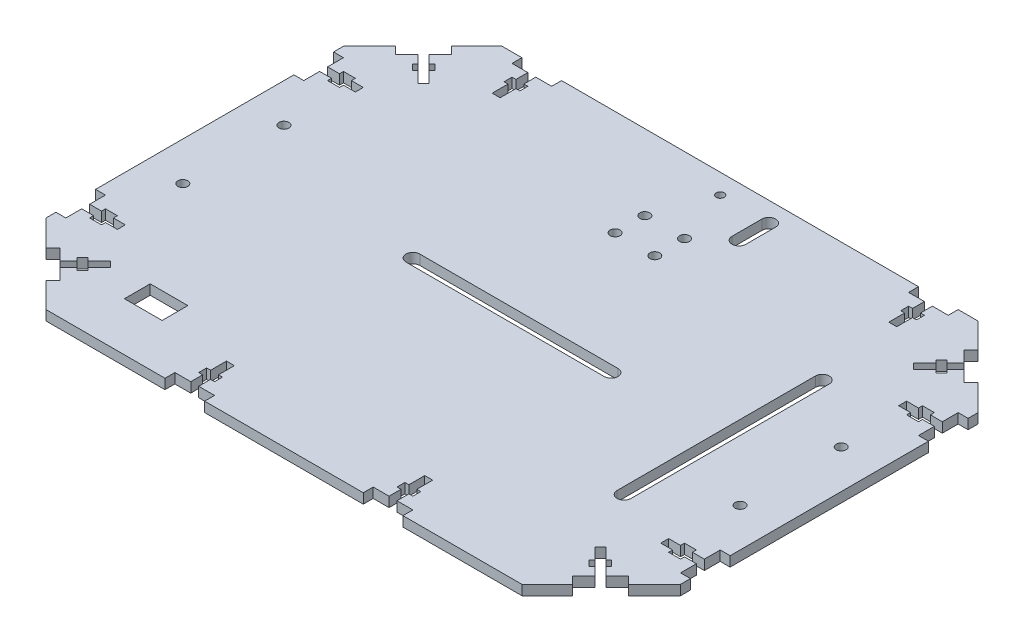
SolidWorks part; units mm, degrees
ref_plane "Front Plane" through (0, 0, 0) normal (0, 0, 1) x (1, 0, 0)
ref_plane "Top Plane" through (0, 0, 0) normal (0, 1, 0) x (1, 0, 0)
ref_plane "Right Plane" through (0, 0, 0) normal (1, 0, 0) x (0, 0, -1)
sketch "Sketch2" plane through (0, 0, 0) normal (0, 1, 0) x (1, 0, 0)
  line L1 (160, -115) -> (-160, -115)
  line L2 (160, -115) -> (160, 115)
  line L3 (160, 115) -> (-160, 115)
  line L4 (-160, -115) -> (-160, 115)
  line L5 (160, -115) -> (-160, 115) construction
  line L6 (160, 115) -> (-160, -115) construction
  point P0 (0, 0)
  dimension "D1" = 230
  dimension "D2" = 320
extrude "Boss-Extrude1" add sketch "Sketch2" along normal blind 5
chamfer "Chamfer1" distance 40 distance2 40 1 edges at (-160, 2.5, -115)
chamfer "Chamfer2" distance 40 distance2 40 1 edges at (160, 2.5, -115)
chamfer "Chamfer3" distance 40 distance2 40 1 edges at (-160, 2.5, 115)
chamfer "Chamfer4" distance 40 distance2 40 1 edges at (160, 2.5, 115)
sketch "Sketch3" plane through (0, 5, 0) normal (0, 1, 0) x (1, 0, 0)
  line L1 (-160, 75) -> (-160, -75) construction
  line L2 (120, 115) -> (-120, 115) construction
  circle A0 centre (-10, 77) radius 2.5
  circle A1 centre (-10, 62) radius 2.5
  dimension "D1" = 5
  dimension "D2" = 5
  dimension "D3" = 38
  dimension "D4" = 150
  dimension "D5" = 150
  dimension "D6" = 15
extrude "Cut-Extrude1" cut sketch "Sketch3" against normal blind 10
mirror "Mirror1" about plane through (0, 0, 0) normal (1, 0, 0) of "Cut-Extrude1"
sketch "Sketch10" plane through (0, 5, 0) normal (0, 1, 0) x (1, 0, 0)
  line L0 (40, -115) -> (60, -115)
  line L1 (40, -115) -> (40, -110)
  line L2 (40, -110) -> (60, -110)
  line L3 (60, -115) -> (60, -110)
  line L4 (48, -110) -> (52, -110)
  line L5 (48, -110) -> (48, -92)
  line L6 (48, -92) -> (52, -92)
  line L7 (52, -110) -> (52, -92)
  line L8 (46, -100) -> (54, -100)
  line L9 (46, -100) -> (46, -104)
  line L10 (46, -104) -> (54, -104)
  line L11 (54, -100) -> (54, -104)
  line L12 (-120, -115) -> (120, -115) construction
  line L13 (160, -75) -> (160, 75) construction
  dimension "D1" = 20
  dimension "D2" = 4
  dimension "D3" = 18
  dimension "D4" = 4
  dimension "D5" = 8
  dimension "D6" = 6
  dimension "D7" = 8
  dimension "D8" = 6
  dimension "D9" = 6
  dimension "D10" = 5
  dimension "D11" = 0
  dimension "D12" = 100
extrude "Cut-Extrude7" cut sketch "Sketch10" against normal blind 10 contours L10 L5 L2 L7 | L5 L10 L7 L8
mirror "Mirror2" about plane through (0, 0, 0) normal (1, 0, 0) of "Cut-Extrude7"
sketch "Sketch11" plane through (0, 5, 0) normal (0, 1, 0) x (1, 0, 0)
  line L1 (90, 115) -> (110, 115)
  line L2 (90, 115) -> (90, 110)
  line L3 (90, 110) -> (110, 110)
  line L4 (110, 115) -> (110, 110)
  line L6 (120, 115) -> (-120, 115) construction
  line L7 (98, 110) -> (102, 110)
  line L8 (98, 110) -> (98, 92)
  line L9 (98, 92) -> (102, 92)
  line L10 (102, 110) -> (102, 92)
  line L11 (96, 104) -> (104, 104)
  line L12 (96, 104) -> (96, 100)
  line L13 (96, 100) -> (104, 100)
  line L14 (104, 104) -> (104, 100)
  line L15 (160, -75) -> (160, 75) construction
  line M55 (120, 115) -> (-120, 115)
  dimension "D1" = 20
  dimension "D2" = 0
  dimension "D3" = 5
  dimension "D4" = 18
  dimension "D5" = 4
  dimension "D6" = 8
  dimension "D7" = 8
  dimension "D8" = 6
  dimension "D9" = 4
  dimension "D10" = 8
  dimension "D11" = 6
  dimension "D12" = 50
extrude "Cut-Extrude8" cut sketch "Sketch11" against normal blind 10 contours L4 L2 L3 M55 | L8 L11 L10 L3 | L8 L13 L10 L11 | L13 L8 L9 L10 | L14 L11 L10 L13 | L12 L13 L8 L11
mirror "Mirror3" about plane through (0, 0, 0) normal (1, 0, 0) of "Cut-Extrude8"
sketch "Sketch13" plane through (0, 5, 0) normal (0, 1, 0) x (1, 0, 0)
  line L0 (-160, 75) -> (-160, -75) construction
  line L1 (-160, -50) -> (-155, -50)
  line L2 (-160, -50) -> (-160, -70)
  line L3 (-160, -70) -> (-155, -70)
  line L4 (-155, -50) -> (-155, -70)
  line L5 (-120, -115) -> (-60, -115) construction
  line L7 (-155, -58) -> (-137, -58)
  line L8 (-155, -58) -> (-155, -62)
  line L9 (-155, -62) -> (-137, -62)
  line L10 (-137, -58) -> (-137, -62)
  line L11 (-149, -56) -> (-143, -56)
  line L12 (-149, -56) -> (-149, -64)
  line L13 (-149, -64) -> (-143, -64)
  line L14 (-143, -56) -> (-143, -64)
  dimension "D1" = 5
  dimension "D2" = 45
  dimension "D3" = 20
  dimension "D4" = 4
  dimension "D5" = 8
  dimension "D6" = 8
  dimension "D7" = 18
  dimension "D8" = 6
  dimension "D9" = 8
  dimension "D10" = 2
  dimension "D11" = 6
  dimension "D12" = 6
extrude "Cut-Extrude9" cut sketch "Sketch13" against normal blind 10 contours L4 L1 L2 L3 | L14 L9 L12 L13 | L14 L11 L12 L7
mirror "Mirror4" about plane through (0, 0, 0) normal (1, 0, 0) of "Cut-Extrude9" second plane through (0, 0, 0) second plane normal (0, 0, 1)
sketch "Sketch14" plane through (0, 5, 0) normal (0, 1, 0) x (1, 0, 0)
  line L0 (-146.8701, -88.1299) -> (-132.7279, -102.2721)
  line L2 (-132.7279, -102.2721) -> (-129.1924, -98.7365)
  line L3 (-129.1924, -98.7365) -> (-143.3345, -84.5944)
  line L4 (-143.3345, -84.5944) -> (-146.8701, -88.1299)
  line L5 (-134.8492, -93.0797) -> (-122.1213, -80.3518)
  line L6 (-122.1213, -80.3518) -> (-124.9497, -77.5233)
  line L7 (-124.9497, -77.5233) -> (-137.6777, -90.2513)
  line L8 (-134.8492, -84.5944) -> (-129.1924, -90.2513)
  line L9 (-134.8492, -84.5944) -> (-132.0208, -81.766)
  line L10 (-132.0208, -81.766) -> (-126.364, -87.4228)
  line L11 (-126.364, -87.4228) -> (-129.1924, -90.2513)
  line L12 (-160, -75) -> (-120, -115) construction
  dimension "D1" = 5
  dimension "D2" = 20
  dimension "D3" = 0
  dimension "D4" = 18
  dimension "D5" = 4
  dimension "D6" = 8
  dimension "D7" = 8
  dimension "D8" = 18
  dimension "D9" = 6
  dimension "D10" = 4
  dimension "D11" = 6
  dimension "D12" = 8
  dimension "D13" = 6
  dimension "D14" = 18.5685
extrude "Cut-Extrude10" cut sketch "Sketch14" against normal blind 10 contours L3 L4 L0 L2 | L8 L7 L3 L5 | L10 L7 L8 L5 | L7 L10 L5 L6 | L11 L10 L5 L8 | L10 L9 L8 L7
mirror "Mirror5" about plane through (0, 0, 0) normal (1, 0, 0) of "Cut-Extrude10" second plane through (0, 0, 0) second plane normal (0, 0, 1)
sketch "Sketch15" plane through (0, 5, 0) normal (0, 1, 0) x (1, 0, 0)
  line L0 (50, 0) -> (-50, 0) construction
  line L1 (50, -3.5) -> (-50, -3.5)
  line L2 (50, 3.5) -> (-50, 3.5)
  line L3 (160, -50) -> (160, 50) construction
  line L4 (-160, 50) -> (-160, -50) construction
  line L5 (-40, -115) -> (40, -115) construction
  line L6 (90, 115) -> (-90, 115) construction
  arc A0 (50, -3.5) -> (50, 3.5) centre (50, 0) ccw
  arc A1 (-50, 3.5) -> (-50, -3.5) centre (-50, 0) ccw
  point P3 (0, 0)
  dimension "D2" = 110
  dimension "D3" = 110
  dimension "D1" = 100
  dimension "D4" = 7
  dimension "D5" = 100
  dimension "D6" = 111.5
  dimension "D7" = 111.5
extrude "Cut-Extrude11" cut sketch "Sketch15" against normal blind 10
sketch "Sketch16" plane through (0, 5, 0) normal (0, 1, 0) x (1, 0, 0)
  line L0 (106.5, 50) -> (106.5, -50) construction
  line L1 (110, 50) -> (110, -50)
  line L2 (103, 50) -> (103, -50)
  line L5 (-110, 115) -> (-120, 115) construction
  line L7 (-120, -115) -> (-60, -115) construction
  line L9 (160, -50) -> (160, 50) construction
  arc A0 (110, 50) -> (103, 50) centre (106.5, 50) ccw
  arc A1 (103, -50) -> (110, -50) centre (106.5, -50) ccw
  point P2 (106.5, 0)
  dimension "D3" = 65
  dimension "D4" = 65
  dimension "D1" = 100
  dimension "D2" = 7
  dimension "D5" = 50
extrude "Cut-Extrude12" cut sketch "Sketch16" against normal blind 10
sketch "Sketch17" plane through (0, 5, 0) normal (0, 1, 0) x (1, 0, 0)
  line L0 (160, -50) -> (160, 50) construction
  line L1 (120, 115) -> (110, 115) construction
  circle A0 centre (140.5, 25.5) radius 2.5
  dimension "D1" = 5
  dimension "D2" = 19.5
  dimension "D3" = 89.5
extrude "Cut-Extrude13" cut sketch "Sketch17" against normal blind 10
mirror "Mirror6" about plane through (0, 0, 0) normal (1, 0, 0) of "Cut-Extrude13" second plane through (0, 0, 0) second plane normal (0, 0, 1)
sketch "Sketch18" plane through (0, 5, 0) normal (0, 1, 0) x (1, 0, 0)
  line L0 (90, 115) -> (-90, 115) construction
  circle A0 centre (0, 105) radius 2
  dimension "D1" = 4
  dimension "D2" = 10
extrude "Cut-Extrude14" cut sketch "Sketch18" against normal blind 8
sketch "Sketch19" plane through (0, 5, 0) normal (0, 1, 0) x (1, 0, 0)
  line L0 (24.4719, 105) -> (24.4719, 90) construction
  line L1 (27.9719, 105) -> (27.9719, 90)
  line L2 (20.9719, 105) -> (20.9719, 90)
  line L3 (90, 115) -> (-90, 115) construction
  arc A0 (27.9719, 105) -> (20.9719, 105) centre (24.4719, 105) ccw
  arc A1 (20.9719, 90) -> (27.9719, 90) centre (24.4719, 90) ccw
  point P2 (24.4719, 97.5)
  dimension "D3" = 10
  dimension "D1" = 7
  dimension "D2" = 15
extrude "Cut-Extrude15" cut sketch "Sketch19" against normal blind 10
sketch "Sketch20" plane through (0, 5, 0) normal (0, 1, 0) x (1, 0, 0)
  line L1 (-104.9628, -77.4939) -> (-85.9628, -77.4939)
  line L2 (-104.9628, -77.4939) -> (-104.9628, -90.4939)
  line L3 (-104.9628, -90.4939) -> (-85.9628, -90.4939)
  line L4 (-85.9628, -77.4939) -> (-85.9628, -90.4939)
  dimension "D1" = 13
  dimension "D2" = 19
extrude "Cut-Extrude16" cut sketch "Sketch20" against normal blind 10
